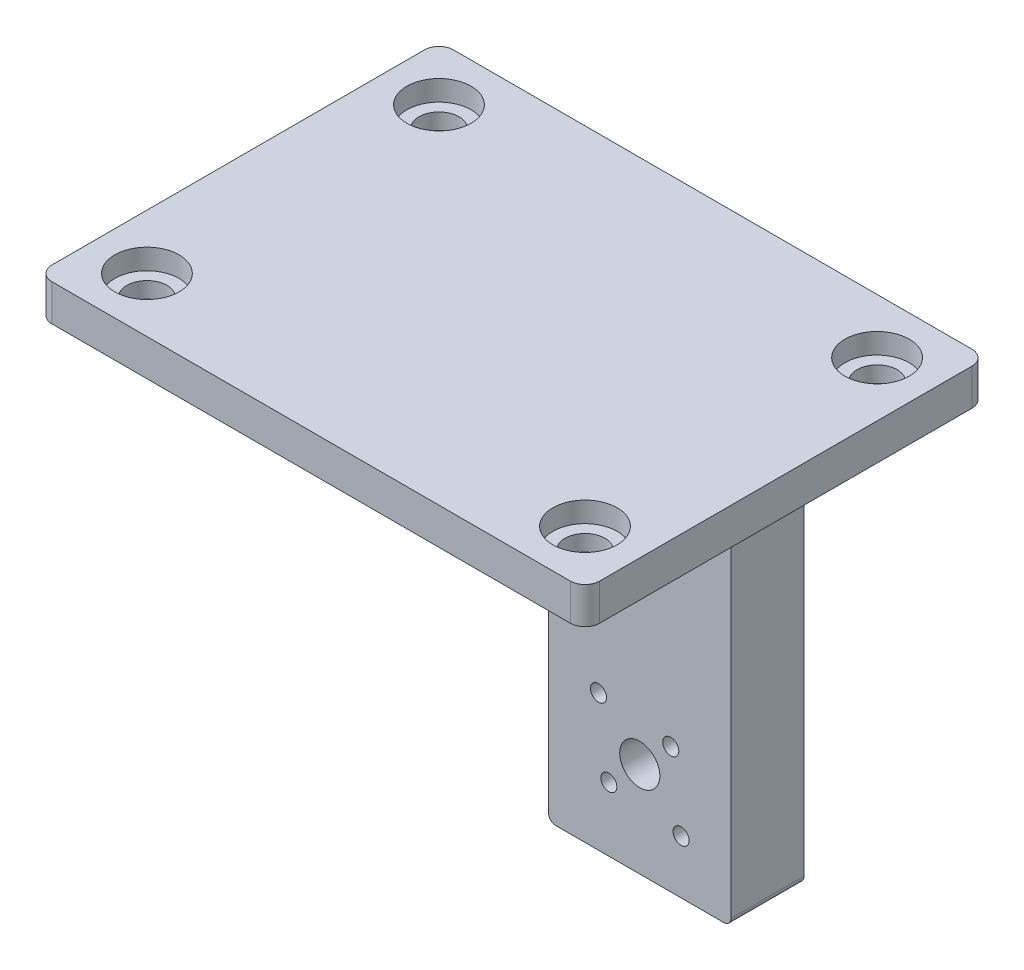
SolidWorks part; units mm, degrees
ref_plane "Front Plane" through (0, 0, 0) normal (0, 0, 1) x (1, 0, 0)
ref_plane "Top Plane" through (0, 0, 0) normal (0, 1, 0) x (1, 0, 0)
ref_plane "Right Plane" through (0, 0, 0) normal (1, 0, 0) x (0, 0, -1)
sketch "Sketch1" plane through (0, 0, 0) normal (0, 1, 0) x (1, 0, 0)
  line L1 (-37.5, -27.5) -> (37.5, -27.5)
  line L2 (-37.5, -27.5) -> (-37.5, 27.5)
  line L3 (-37.5, 27.5) -> (37.5, 27.5)
  line L4 (37.5, -27.5) -> (37.5, 27.5)
  line L5 (-37.5, -27.5) -> (37.5, 27.5) construction
  line L6 (-37.5, 27.5) -> (37.5, -27.5) construction
  point P1 (0, 0)
  dimension "D1" = 55
  dimension "D2" = 75
extrude "Boss-Extrude1" add sketch "Sketch1" along normal blind 5
sketch "Sketch2" plane through (0, 5, 0) normal (0, 1, 0) x (1, 0, 0)
  line L0 (-30, 20) -> (-30, -20) construction
  circle A0 centre (-30, 20) radius 2.75
  circle A1 centre (-30, -20) radius 2.75
  point P4 (-30, 0)
  dimension "D1" = 5.5
  dimension "D2" = 5.5
  dimension "D3" = 40
  dimension "D4" = 30
extrude "Cut-Extrude1" cut sketch "Sketch2" against normal through all
mirror "Mirror1" about plane through (0, 0, 0) normal (1, 0, 0) of "Cut-Extrude1"
fillet "Fillet5" radius 2 4 edges at (-37.5, 2.5, 27.5) (37.5, 2.5, 27.5) (37.5, 2.5, -27.5) (-37.5, 2.5, -27.5)
sketch "Sketch6" plane through (0, 5, 0) normal (0, 1, 0) x (1, 0, 0)
  circle A0 centre (-30, 20) radius 4.4
  circle A1 centre (-30, -20) radius 4.4
  circle A2 centre (30, 20) radius 4.4
  circle A3 centre (30, -20) radius 4.4
  dimension "D1" = 8.8
  dimension "D2" = 8.8
  dimension "D3" = 8.8
  dimension "D4" = 8.8
extrude "Cut-Extrude3" cut sketch "Sketch6" against normal offset from surface (2.8 mm away) 2.2 up to face at (30, 0, -17.25)
sketch "Sketch7" plane through (0, 0, 0) normal (0, -1, 0) x (1, 0, 0)
  line L0 (35.5, -27.5) -> (-35.5, -27.5) construction
  line L1 (-12.5, -27.5) -> (12.5, -27.5)
  line L2 (-12.5, -27.5) -> (-12.5, -17.5)
  line L3 (-12.5, -17.5) -> (12.5, -17.5)
  line L4 (12.5, -27.5) -> (12.5, -17.5)
  point P6 (0, -17.5)
  dimension "D1" = 10
  dimension "D2" = 25
extrude "Boss-Extrude2" add sketch "Sketch7" along normal blind 70
sketch "Sketch8" plane through (-12.5, 0, 0) normal (-1, 0, 0) x (0, 0, 1)
  line L0 (-27.5, -70) -> (-27.5, 0) construction
  line L1 (-17.5, -70) -> (-24.5, -70)
  line L2 (-17.5, -70) -> (-17.5, -40)
  line L3 (-17.5, -40) -> (-24.5, -40)
  line L4 (-24.5, -70) -> (-24.5, -40)
  dimension "D1" = 3
  dimension "D2" = 30
extrude "Cut-Extrude4" cut sketch "Sketch8" against normal through all
sketch "Sketch11" plane through (0, -40, 0) normal (0, -1, 0) x (1, 0, 0)
  line L1 (-12.5, -17.5) -> (12.5, -17.5)
  line L2 (-12.5, -17.5) -> (-12.5, -24.5)
  line L3 (-12.5, -24.5) -> (12.5, -24.5)
  line L4 (12.5, -17.5) -> (12.5, -24.5)
extrude "Boss-Extrude3" add sketch "Sketch11" along normal up to surface (30 mm away) up to face at (0, -70, -26)
fillet "Fillet6" radius 2 3 edges at (12.5, 0, -22.5) (0, 0, -17.5) (-12.5, 0, -22.5)
fillet "Fillet7" radius 1 2 edges at (12.5, -70, -22.5) (-12.5, -70, -22.5)
sketch "Sketch17" plane through (0, 0, -27.5) normal (0, 0, -1) x (-1, 0, 0)
  line L0 (0, -97.8991) -> (0, -22.8991) construction
  line L3 (0, -57) -> (5.6569, -51.3431) construction
  line L4 (-5.6569, -62.6569) -> (0, -57) construction
  line L5 (-4.2426, -52.7574) -> (0, -57) construction
  line L6 (0, -57) -> (4.2426, -61.2426) construction
  line L7 (11.5, -70) -> (-11.5, -70) construction
  circle A0 centre (0, -57) radius 2.75
  circle A1 centre (5.6569, -51.3431) radius 1.1
  circle A2 centre (-5.6569, -62.6569) radius 1.1
  circle A3 centre (-4.2426, -52.7574) radius 1.1
  circle A4 centre (4.2426, -61.2426) radius 1.1
  dimension "D1" = 5.5
  dimension "D2" = 13
  dimension "D3" = 2.2
  dimension "D5" = 2.2
  dimension "D8" = 2.2
  dimension "D10" = 2.2
  dimension "D12" = 12
  dimension "D4" = 45
  dimension "D6" = 45
  dimension "D7" = 16
  dimension "D9" = 45
  dimension "D11" = 45
extrude "Cut-Extrude5" cut sketch "Sketch17" against normal through all
sketch "Sketch18" plane through (0, 0, -27.5) normal (0, 0, -1) x (-1, 0, 0)
  circle A0 centre (-4.2426, -52.7574) radius 2.5
  circle A1 centre (-5.6569, -62.6569) radius 2.5
  circle A2 centre (5.6569, -51.3431) radius 2.5
  circle A3 centre (4.2426, -61.2426) radius 2.5
  dimension "D1" = 5
  dimension "D2" = 5
  dimension "D3" = 5
  dimension "D4" = 5
extrude "Cut-Extrude6" cut sketch "Sketch18" against normal offset from surface (7 mm away) 3 up to face at (-6.7569, -51.3431, -17.5)
